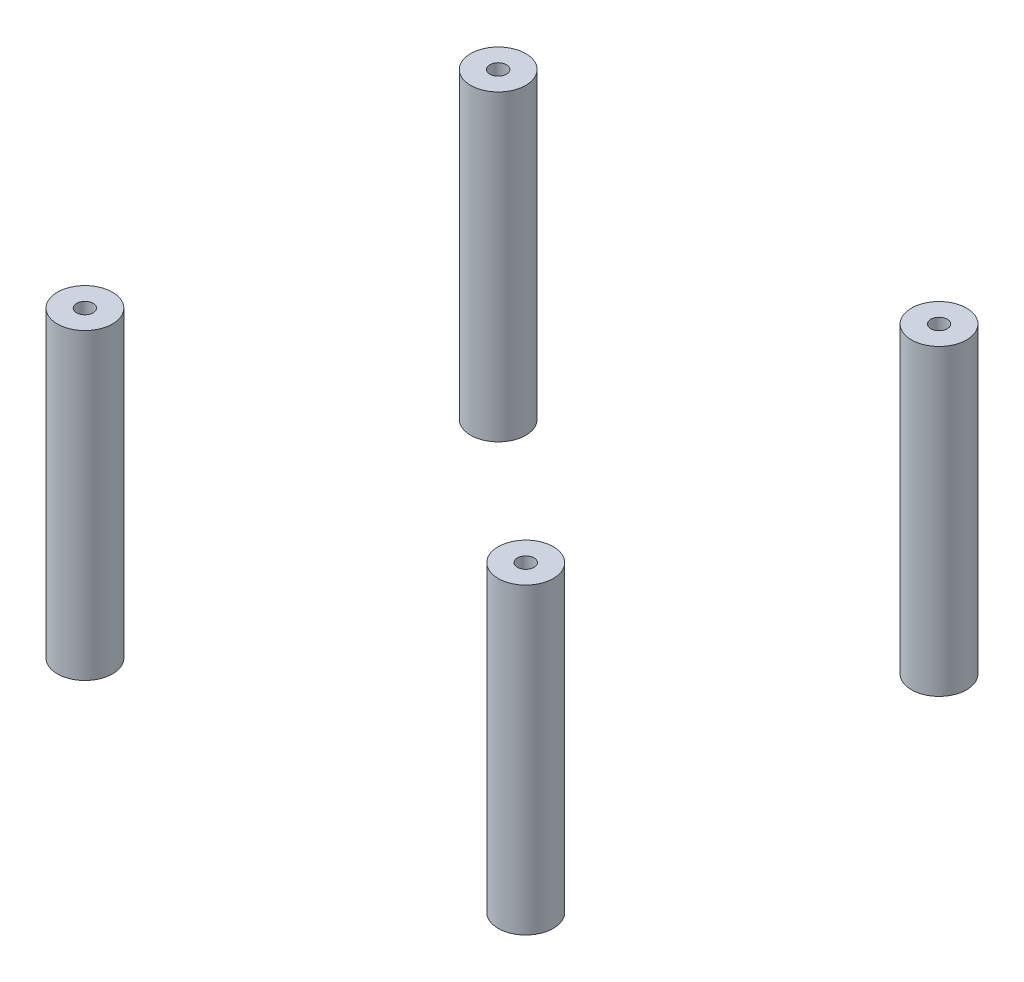
SolidWorks part; units mm, degrees
ref_plane "Front Plane" through (0, 0, 0) normal (0, 0, 1) x (1, 0, 0)
ref_plane "Top Plane" through (0, 0, 0) normal (0, 1, 0) x (1, 0, 0)
ref_plane "Right Plane" through (0, 0, 0) normal (1, 0, 0) x (0, 0, -1)
sketch "Sketch1" plane through (0, 0, 0) normal (0, 1, 0) x (1, 0, 0)
  line L0 (-40, 37.5) -> (40, 37.5) construction
  line L1 (40, 37.5) -> (40, -37.5) construction
  line L2 (40, -37.5) -> (-40, -37.5) construction
  line L3 (-40, -37.5) -> (-40, 37.5) construction
  line L4 (-40, 37.5) -> (40, -37.5) construction
  circle A0 centre (-40, 37.5) radius 5
  circle A1 centre (40, 37.5) radius 5
  circle A2 centre (40, -37.5) radius 5
  circle A3 centre (-40, -37.5) radius 5
  circle A4 centre (-40, 37.5) radius 1.5
  circle A5 centre (40, 37.5) radius 1.5
  circle A6 centre (40, -37.5) radius 1.5
  circle A7 centre (-40, -37.5) radius 1.5
extrude "Boss-Extrude1" add sketch "Sketch1" along normal blind 55
